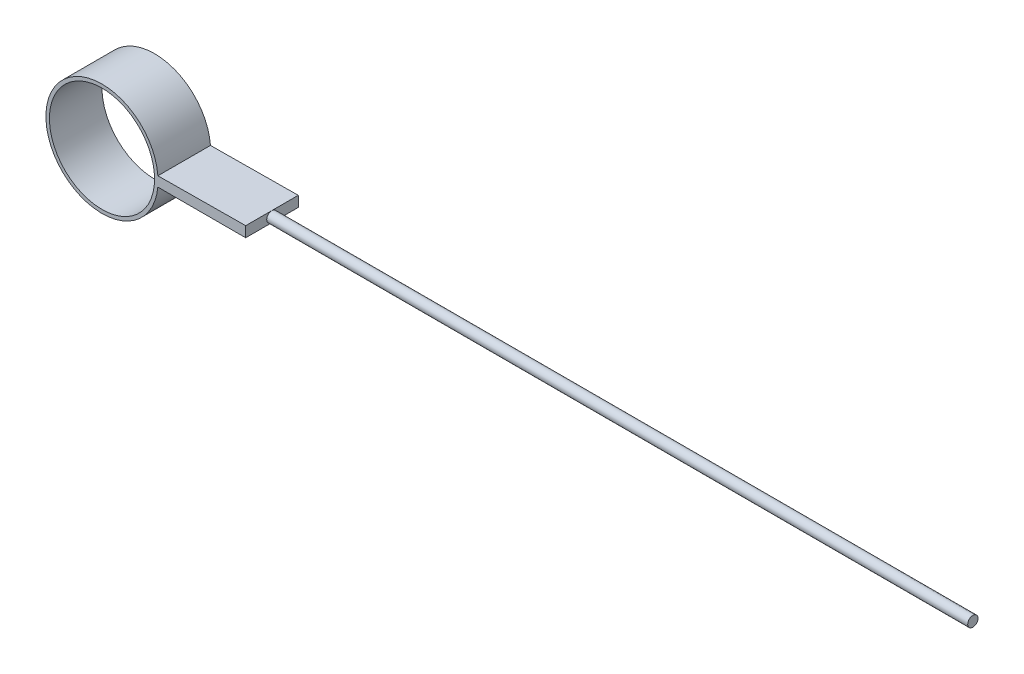
SolidWorks part; units mm, degrees
ref_plane "前视基准面" through (0, 0, 0) normal (0, 0, 1) x (1, 0, 0)
ref_plane "上视基准面" through (0, 0, 0) normal (0, 1, 0) x (1, 0, 0)
ref_plane "右视基准面" through (0, 0, 0) normal (1, 0, 0) x (0, 0, -1)
other "Configuration Table"
sketch "草图1" plane through (0, 0, 0) normal (0, 0, 1) x (1, 0, 0)
  line L0 (3.2, 0) -> (8.2, 0)
  line L1 (8.2, 0) -> (8.2, 0.3)
  line L2 (8.2, 0.3) -> (3.1895, 0.2588)
  line L3 (8.2, 0) -> (8.2, -0.3)
  line L4 (8.2, -0.3) -> (3.1859, -0.3)
  line L5 (-11.8, 0.3) -> (-11.8141, 0.3)
  circle A0 centre (0, 0) radius 3
  circle A1 centre (0, 0) radius 3.2
  dimension "D1" = 0.3
  dimension "D2" = 5
  dimension "D3" = 0.3
extrude "凸台-拉伸1" add sketch "草图1" along normal blind 3
sketch "草图2" plane through (8.2, 0, 0) normal (1, 0, 0) x (0, 0, -1)
  line L0 (0, 0) -> (-3, 0) construction
  line L2 (-1.5, 0.3) -> (-1.5, -0.3398) construction
  circle A2 centre (-1.5061, 0) radius 0.2931
extrude "凸台-拉伸2" add sketch "草图2" along normal blind 40
scale "缩放比例1" scale about centroid uniform scaling yes scale factor 3.5
